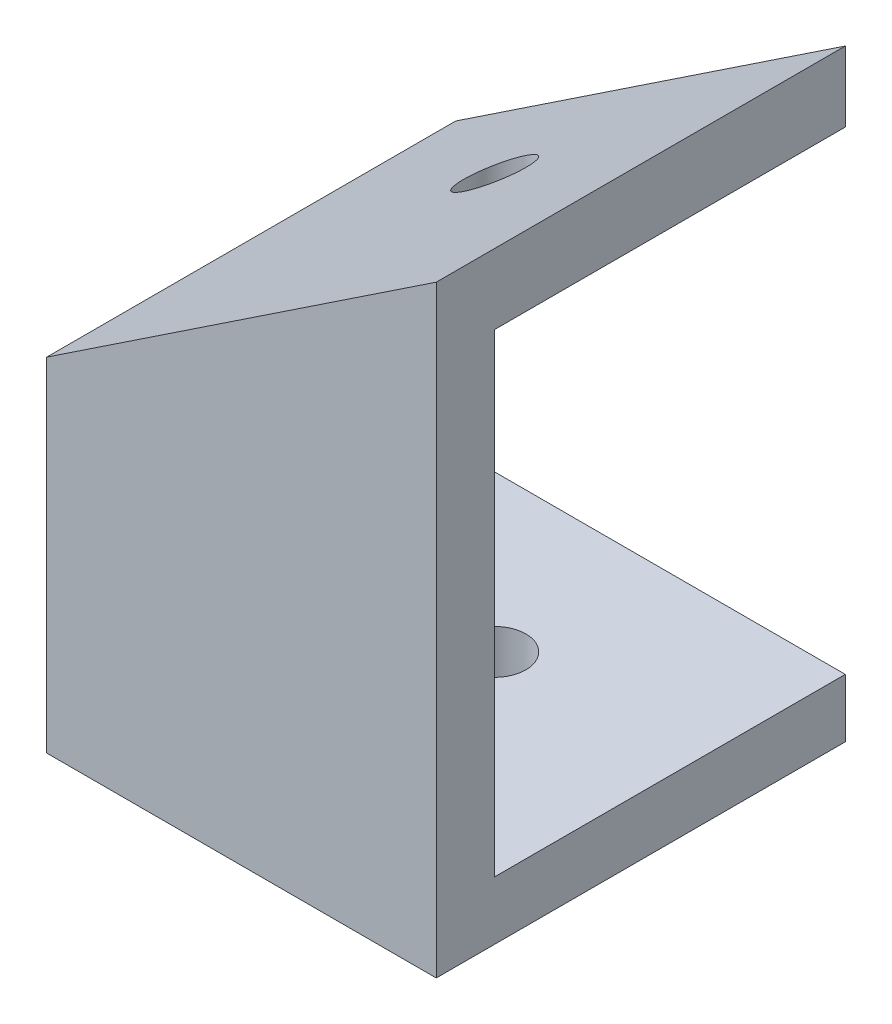
SolidWorks part; units mm, degrees
ref_plane "前视基准面" through (0, 0, 0) normal (0, 0, 1) x (1, 0, 0)
ref_plane "上视基准面" through (0, 0, 0) normal (0, 1, 0) x (1, 0, 0)
ref_plane "右视基准面" through (0, 0, 0) normal (1, 0, 0) x (0, 0, -1)
sketch "草图1" plane through (0, 0, 0) normal (0, 0, 1) x (1, 0, 0)
  line L1 (-7.6343, -2.9061) -> (-7.6343, 8.0939)
  line L2 (-7.6343, 8.0939) -> (7.3657, 8.0939) construction
  line L3 (7.3657, 8.0939) -> (7.3657, 18.0939) construction
  line L4 (-7.6343, 8.0939) -> (7.3657, 18.0939) construction
  line L5 (-7.6343, 8.0939) -> (12.3657, 21.4272)
  line L6 (12.3657, 2.0939) -> (12.3657, 21.4665) construction
  line L8 (12.3657, -5.9061) -> (-7.6343, -5.9061)
  line L9 (-7.6343, -2.9061) -> (-7.6343, -5.9061)
  line L10 (12.3657, 21.4272) -> (12.3657, -5.9061)
  dimension "D1" = 11
  dimension "D2" = 10
  dimension "15" = 15
  dimension "D3" = 5
extrude "凸台-拉伸1" add sketch "草图1" along normal blind 3
sketch "草图2" plane through (0, 0, 3) normal (0, 0, 1) x (1, 0, 0)
  line L0 (-7.6343, 8.0939) -> (12.3657, 21.4272)
  line L1 (-7.6343, 11.6994) -> (12.3657, 25.0327)
  line L2 (-7.6343, 8.0939) -> (-7.6343, -5.9061) construction
  line L3 (12.3657, -5.9061) -> (12.3657, 21.4272) construction
  line L4 (-7.6343, 8.0939) -> (-7.6343, 11.6994)
  line L5 (12.3657, 21.4272) -> (12.3657, 25.0327)
  line L6 (-7.6343, -5.9061) -> (-7.6343, -2.9061)
  line L7 (-7.6343, -2.9061) -> (12.3657, -2.9061)
  line L8 (12.3657, -2.9061) -> (12.3657, -5.9061)
  line L9 (12.3657, -5.9061) -> (-7.6343, -5.9061)
  dimension "D1" = 3
  dimension "D2" = 3
extrude "凸台-拉伸2" add sketch "草图2" along normal blind 18 and the other way blind 3
sketch "草图5" plane through (0, -5.9061, 0) normal (0, -1, 0) x (1, 0, 0)
  line L1 (-7.6343, 0) -> (12.3657, 0) construction
  circle A0 centre (2.3657, 8) radius 1.6
  dimension "D1" = 8
extrude "切除-拉伸1" cut sketch "草图5" against normal through all
sketch "草图6" plane through (0, 0, 3) normal (0, 0, 1) x (1, 0, 0)
  line L0 (-7.6343, 8.0939) -> (-7.6343, -2.9061)
  line L1 (-7.6343, -2.9061) -> (12.3657, -2.9061)
  line L2 (-7.6343, -2.9061) -> (12.3657, -2.9061) construction
  line L3 (12.3657, -5.9061) -> (12.3657, -2.9061) construction
  line L4 (12.3657, -2.9061) -> (12.3657, 21.4272)
  line L5 (12.3657, 21.4272) -> (-7.6343, 8.0939)
extrude "切除-拉伸2" cut sketch "草图6" against normal through all
sketch "草图7" plane through (0, 0, 21) normal (0, 0, 1) x (1, 0, 0)
  line L0 (-7.6343, 11.6994) -> (-7.6343, -5.9061)
  line L1 (-7.6343, -5.9061) -> (12.3657, -5.9061)
  line L2 (-7.6343, -5.9061) -> (12.3657, -5.9061) construction
  line L3 (12.3657, -5.9061) -> (12.3657, -2.9061) construction
  line L4 (12.3657, -5.9061) -> (12.3657, 25.0327)
  line L5 (12.3657, 21.4272) -> (12.3657, 25.0327) construction
  line L6 (12.3657, 25.0327) -> (-7.6343, 11.6994)
  line L7 (12.3657, 48.4241) -> (12.3657, -5.9061) construction
extrude "凸台-拉伸3" add sketch "草图7" against normal blind 3
